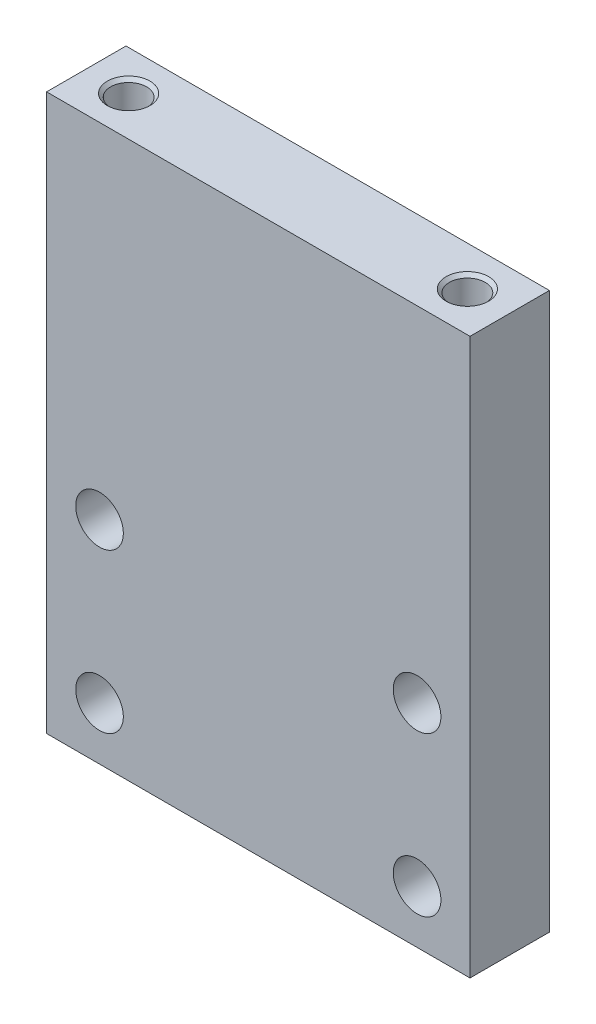
SolidWorks part; units mm, degrees
ref_plane "前视基准面" through (0, 0, 0) normal (0, 0, 1) x (1, 0, 0)
ref_plane "上视基准面" through (0, 0, 0) normal (0, 1, 0) x (1, 0, 0)
ref_plane "右视基准面" through (0, 0, 0) normal (1, 0, 0) x (0, 0, -1)
sketch "草图1" plane through (0, 0, 0) normal (0, 0, 1) x (1, 0, 0)
  line L1 (-40, 52.5) -> (40, 52.5)
  line L2 (-40, 52.5) -> (-40, -52.5)
  line L3 (-40, -52.5) -> (40, -52.5)
  line L4 (40, 52.5) -> (40, -52.5)
  line L5 (-40, 52.5) -> (40, -52.5) construction
  line L6 (-40, -52.5) -> (40, 52.5) construction
  line L7 (-30, -12.5) -> (30, -12.5) construction
  line L8 (-30, -12.5) -> (-30, -42.5) construction
  line L9 (-30, -42.5) -> (30, -42.5) construction
  line L10 (30, -12.5) -> (30, -42.5) construction
  circle A0 centre (-30, -12.5) radius 4.5
  circle A1 centre (30, -12.5) radius 4.5
  circle A2 centre (30, -42.5) radius 4.5
  circle A3 centre (-30, -42.5) radius 4.5
  point P0 (0, 0)
  point P14 (0, -12.5)
  dimension "D3" = 9
  dimension "D1" = 80
  dimension "D2" = 105
  dimension "D4" = 0
  dimension "D5" = 60
  dimension "D6" = 30
  dimension "D7" = 20
extrude "凸台-拉伸1" add sketch "草图1" along normal blind 15
sketch "草图2" plane through (0, 52.5, 0) normal (0, 1, 0) x (1, 0, 0)
  line L0 (-32, -7.5) -> (32, -7.5) construction
  line L1 (0, 13.3967) -> (0, -39.7953) construction
  line L4 (40, -15) -> (-40, -15) construction
  circle A0 centre (-32, -7.5) radius 3.4
  circle A1 centre (32, -7.5) radius 3.4
  point P8 (0, -7.5)
  dimension "D1" = 6.8
  dimension "D3" = 0
  dimension "D2" = 64
  dimension "D4" = 7.5
hole_wizard "M8 螺纹孔1" positions "3D草图1" profile "草图3" tap size "M8" standard "GB"
sketch3d "3D草图1"
  point P0 (-32, 52.5, 7.5)
  point P3 (32, 52.5, 7.5)
sketch "草图3" plane through (-32, 52.5, 7.5) normal (1, 0, 0) x (0, 0, 1)
  line L0 (0, 0) -> (0, 24.2929)
  line L1 (0, 24.2929) -> (3.4, 22.25)
  line L2 (3.4, 22.25) -> (3.4, 0.625)
  line L3 (3.4, 0.625) -> (4.025, 0)
  line L5 (4.025, 0) -> (0, 0)
  line L6 (-3.4, 0.625) -> (-4.025, 0) construction
  line L10 (0, 24.2929) -> (-3.4, 22.25) construction
  line L11 (0, -6.35) -> (0, 107.95) construction
  dimension "螺纹孔钻头直径" = 6.8
  dimension "螺纹孔钻头深度" = 22.25
  dimension "近端锥形沉头孔直径" = 8.05
  dimension "近端锥形沉头孔角度" = 90
  dimension "导头角度" = 118
cosmetic thread "孔螺蚊线1"
cosmetic thread "孔螺蚊线2"
